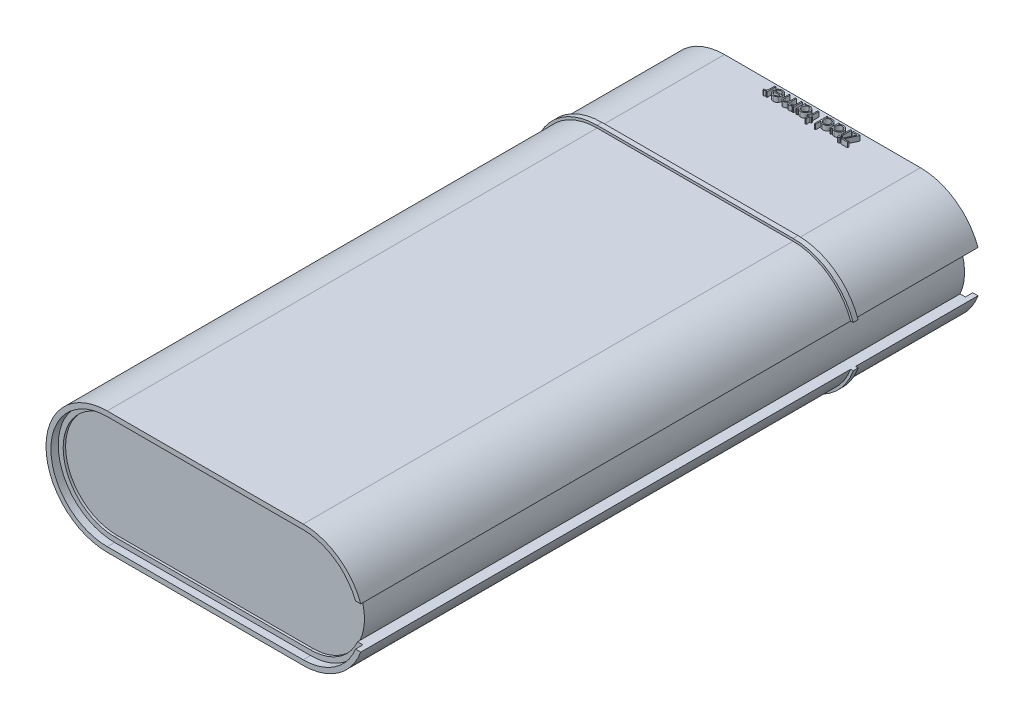
SolidWorks part; units mm, degrees
ref_plane "Front Plane" through (0, 0, 0) normal (0, 0, 1) x (1, 0, 0)
ref_plane "Top Plane" through (0, 0, 0) normal (0, 1, 0) x (1, 0, 0)
ref_plane "Right Plane" through (0, 0, 0) normal (1, 0, 0) x (0, 0, -1)
sketch "Sketch6" plane through (0, 0, 0) normal (0, 0, 1) x (1, 0, 0)
  line L0 (-40, 0) -> (40, 0) construction
  line L1 (-40, 25) -> (40, 25)
  line L2 (-40, -25) -> (40, -25)
  arc A0 (-40, 25) -> (-40, -25) centre (-40, 0) ccw
  arc A1 (40, -25) -> (40, 25) centre (40, 0) ccw
  point P2 (0, 0)
  dimension "D1" = 80
  dimension "D2" = 25
  dimension "D3" = 50
extrude "Boss-Extrude2" add sketch "Sketch6" along normal blind 50
sketch "Sketch12" plane through (0, 0, 0) normal (0, 0, -1) x (-1, 0, 0)
  line L4 (40, 23) -> (-40, 23)
  line L5 (-40, -23) -> (40, -23)
  line L6 (40, 23) -> (-40, 23)
  line L7 (-40, -23) -> (40, -23)
  arc A4 (40, -23) -> (40, 23) centre (40, 0) ccw
  arc A5 (-40, 23) -> (-40, -23) centre (-40, 0) ccw
  arc A6 (40, -23) -> (40, 23) centre (40, 0) ccw
  arc A7 (-40, 23) -> (-40, -23) centre (-40, 0) ccw
  dimension "D1" = 2
extrude "Cut-Extrude8" cut sketch "Sketch12" against normal blind 3
sketch "Sketch13" plane through (0, 0, 50) normal (0, 0, 1) x (1, 0, 0)
  line L4 (-40, -26) -> (40, -26)
  line L5 (40, 26) -> (-40, 26)
  line L6 (-40, -26) -> (40, -26)
  line L7 (40, 26) -> (-40, 26)
  arc A4 (-40, 26) -> (-40, -26) centre (-40, 0) ccw
  arc A5 (40, -26) -> (40, 26) centre (40, 0) ccw
  arc A6 (-40, 26) -> (-40, -26) centre (-40, 0) ccw
  arc A7 (40, -26) -> (40, 26) centre (40, 0) ccw
  dimension "D1" = 1
extrude "Boss-Extrude3" add sketch "Sketch13" along normal blind 2
sketch "Sketch14" plane through (0, 0, 52) normal (0, 0, 1) x (1, 0, 0)
  line L4 (-40, -25) -> (40, -25)
  line L5 (40, 25) -> (-40, 25)
  line L6 (-40, -25) -> (40, -25)
  line L7 (40, 25) -> (-40, 25)
  arc A4 (-40, 25) -> (-40, -25) centre (-40, 0) ccw
  arc A5 (40, -25) -> (40, 25) centre (40, 0) ccw
  arc A6 (-40, 25) -> (-40, -25) centre (-40, 0) ccw
  arc A7 (40, -25) -> (40, 25) centre (40, 0) ccw
  dimension "D1" = 1
extrude "Boss-Extrude4" add sketch "Sketch14" along normal blind 200
sketch "Sketch16" plane through (0, 0, 252) normal (0, 0, 1) x (1, 0, 0)
  line L6 (-40, -23) -> (40, -23)
  line L7 (40, 23) -> (-40, 23)
  line L8 (-40, -23) -> (40, -23)
  line L9 (40, 23) -> (-40, 23)
  arc A6 (-40, 23) -> (-40, -23) centre (-40, 0) ccw
  arc A7 (40, -23) -> (40, 23) centre (40, 0) ccw
  arc A8 (-40, 23) -> (-40, -23) centre (-40, 0) ccw
  arc A9 (40, -23) -> (40, 23) centre (40, 0) ccw
  dimension "D1" = 2
extrude "Cut-Extrude9" cut sketch "Sketch16" against normal blind 3
ref_plane "Plane1" through (0, 0, -10) normal (0, 0, -1) x (-1, 0, 0)
sketch "Sketch26" plane through (0, 0, 249) normal (0, 0, 1) x (1, 0, 0)
  line L4 (-40, -21) -> (40, -21)
  line L5 (40, 21) -> (-40, 21)
  line L6 (-40, -21) -> (40, -21)
  line L7 (40, 21) -> (-40, 21)
  arc A4 (-40, 21) -> (-40, -21) centre (-40, 0) ccw
  arc A5 (40, -21) -> (40, 21) centre (40, 0) ccw
  arc A6 (-40, 21) -> (-40, -21) centre (-40, 0) ccw
  arc A7 (40, -21) -> (40, 21) centre (40, 0) ccw
  dimension "D1" = 2
extrude "Cut-Extrude14" cut sketch "Sketch26" against normal blind 200 contours A6 L6 A7 L7
sketch "Sketch27" plane through (0, 0, 3) normal (0, 0, -1) x (-1, 0, 0)
  line L4 (40, 21) -> (-40, 21)
  line L5 (-40, -21) -> (40, -21)
  line L6 (40, 21) -> (-40, 21)
  line L7 (-40, -21) -> (40, -21)
  arc A4 (40, -21) -> (40, 21) centre (40, 0) ccw
  arc A5 (-40, 21) -> (-40, -21) centre (-40, 0) ccw
  arc A6 (40, -21) -> (40, 21) centre (40, 0) ccw
  arc A7 (-40, 21) -> (-40, -21) centre (-40, 0) ccw
  dimension "D1" = 2
extrude "Cut-Extrude15" cut sketch "Sketch27" against normal blind 200
sketch "Sketch31" plane through (0, 0, -10) normal (0, 0, -1) x (-1, 0, 0)
  line L1 (-70.8381, -8.527) -> (-51.1619, -8.527)
  line L2 (-70.8381, -8.527) -> (-70.8381, 8.527)
  line L3 (-70.8381, 8.527) -> (-51.1619, 8.527)
  line L4 (-51.1619, -8.527) -> (-51.1619, 8.527)
  line L5 (-70.8381, -8.527) -> (-51.1619, 8.527) construction
  line L6 (-70.8381, 8.527) -> (-51.1619, -8.527) construction
  arc A0 (-40, 21) -> (-40, -21) centre (-40, 0) ccw construction
  point P0 (-61, 0)
extrude "Cut-Extrude16" cut sketch "Sketch31" against normal blind 500
sketch "Sketch34" plane through (0, 0, 3) normal (0, 0, -1) x (-1, 0, 0)
  line L4 (40, 21) -> (-40, 21)
  line L5 (-40, -21) -> (40, -21)
  line L6 (40, 21) -> (-40, 21)
  line L7 (-40, -21) -> (40, -21)
  arc A4 (40, -21) -> (40, 21) centre (40, 0) ccw
  arc A5 (-40, 21) -> (-40, -21) centre (-40, 0) ccw
  arc A6 (40, -21) -> (40, 21) centre (40, 0) ccw
  arc A7 (-40, 21) -> (-40, -21) centre (-40, 0) ccw
  dimension "D1" = 4
ref_plane "Plane2" [suppressed] through (0, 25, 0) normal (0, 1, 0) x (1, 0, 0)
extrude "Boss-Extrude5" add sketch "Sketch34" against normal blind 245 contours L6 A7 L7 A6
sketch "Sketch35" plane through (0, 25, 0) normal (0, 1, 0) x (1, 0, 0)
  line L0 (-31.6069, -2.8698) -> (32.2922, -2.8698) construction
  text T0 "Ziad tamer" font "Century Gothic" height 5
extrude "Boss-Extrude7" add sketch "Sketch35" along normal blind 2
